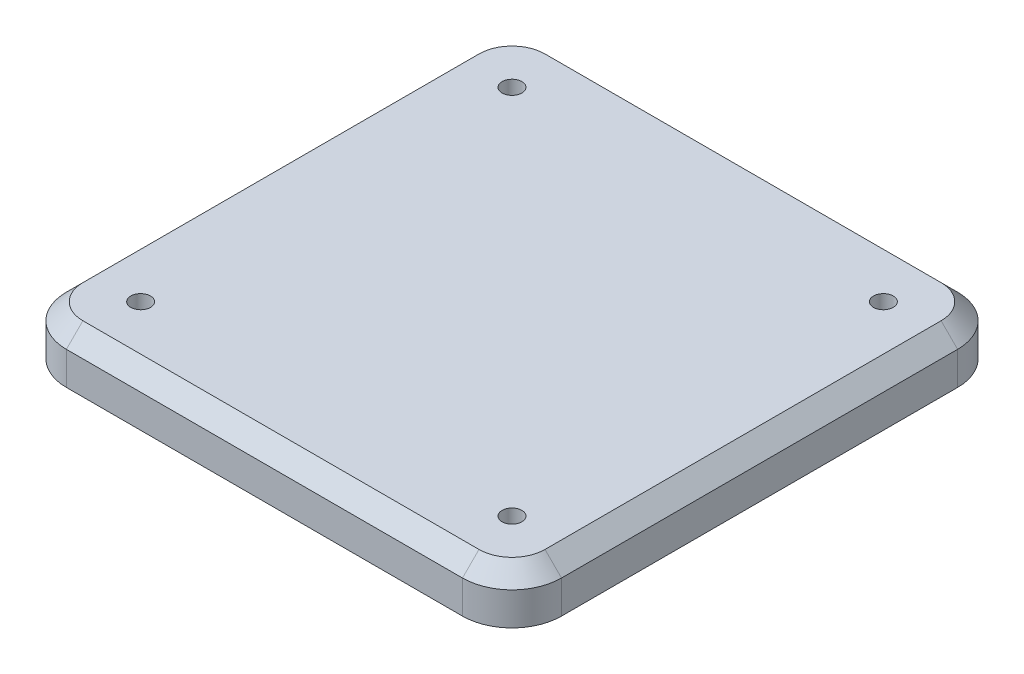
SolidWorks part; units mm, degrees
material "PET"
ref_plane "Alzado" through (0, 0, 0) normal (0, 0, 1) x (1, 0, 0)
ref_plane "Planta" through (0, 0, 0) normal (0, 1, 0) x (1, 0, 0)
ref_plane "Vista lateral" through (0, 0, 0) normal (1, 0, 0) x (0, 0, -1)
sketch "Croquis1" plane through (0, 0, 0) normal (0, 1, 0) x (1, 0, 0)
  line L1 (-150, -150) -> (150, -150)
  line L2 (-150, -150) -> (-150, 150)
  line L3 (-150, 150) -> (150, 150)
  line L4 (150, -150) -> (150, 150)
  line L5 (-150, -150) -> (150, 150) construction
  line L6 (-150, 150) -> (150, -150) construction
  point P0 (0, 0)
  dimension "D1" = 300
  dimension "D2" = 300
extrude "Saliente-Extruir1" add sketch "Croquis1" along normal blind 30
fillet "Redondeo1" radius 30 4 edges at (-150, 15, -150) (150, 15, -150) (150, 15, 150) (-150, 15, 150)
chamfer "Chaflán1" distance 10 angle 45 8 edges at (141.2132, 30, -141.2132) (150, 30, 0) (141.2132, 30, 141.2132) (0, 30, 150) (-141.2132, 30, 141.2132) (-150, 30, 0) (-141.2132, 30, -141.2132) (0, 30, -150)
sketch "Croquis3" plane through (0, 0, 0) normal (0, -1, 0) x (1, 0, 0)
  line L1 (-125, -125) -> (125, -125) construction
  line L2 (-125, -125) -> (-125, 125) construction
  line L3 (-125, 125) -> (125, 125) construction
  line L4 (125, -125) -> (125, 125) construction
  line L5 (-125, -125) -> (125, 125) construction
  line L6 (-125, 125) -> (125, -125) construction
  circle A0 centre (125, -125) radius 6
  circle A1 centre (125, 125) radius 6
  circle A2 centre (-125, 125) radius 6
  circle A3 centre (-125, -125) radius 6
  point P0 (0, 0)
  dimension "D1" = 12
  dimension "D2" = 250
extrude "Cortar-Extruir2" cut sketch "Croquis3" against normal blind 10
sketch "Croquis10" [suppressed] plane through (0, 30, 0) normal (0, 1, 0) x (1, 0, 0)
  circle A0 centre (0, 0) radius 6
  dimension "D1" = 12
extrude "Cortar-Extruir4" [suppressed] cut sketch "Croquis10" against normal blind 10
sketch "Croquis11" plane through (0, 30, 0) normal (0, 1, 0) x (1, 0, 0)
  line L1 (-112.5, -112.5) -> (112.5, -112.5) construction
  line L2 (-112.5, -112.5) -> (-112.5, 112.5) construction
  line L3 (-112.5, 112.5) -> (112.5, 112.5) construction
  line L4 (112.5, -112.5) -> (112.5, 112.5) construction
  line L5 (-112.5, -112.5) -> (112.5, 112.5) construction
  line L6 (-112.5, 112.5) -> (112.5, -112.5) construction
  circle A0 centre (112.5, -112.5) radius 6
  circle A1 centre (112.5, 112.5) radius 6
  circle A2 centre (-112.5, 112.5) radius 6
  circle A3 centre (-112.5, -112.5) radius 6
  point P0 (0, 0)
  dimension "D2" = 12
  dimension "D1" = 225
extrude "Cortar-Extruir5" cut sketch "Croquis11" against normal blind 10
equation "\"A\"= 300mm"
equation "\"B\"= 225mm"
equation "\"C\"= 250mm"
equation "\"D\"= 30mm"
equation "\"D1@Croquis1\"=\"A\""
equation "\"D2@Croquis1\"=\"A\""
equation "\"D2@Croquis3\"=\"C\""
equation "\"D1@Croquis11\"=\"B\""
